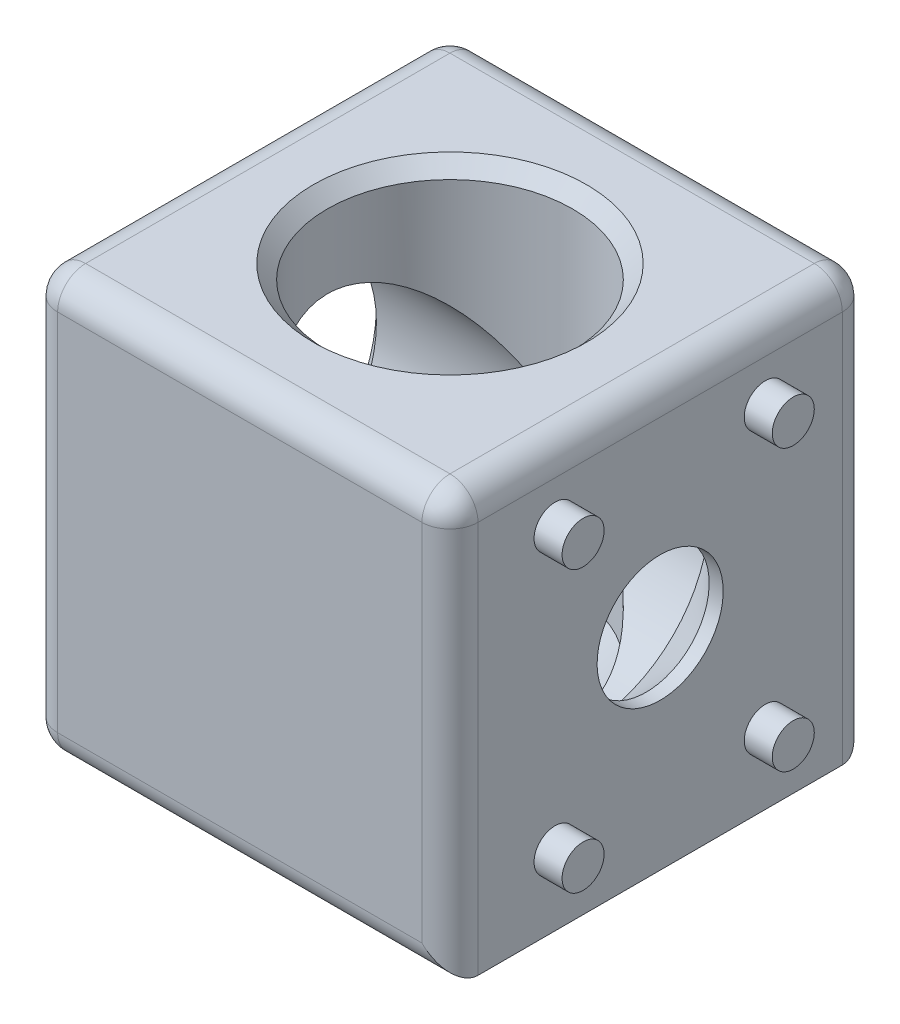
SolidWorks part; units mm, degrees
material "Алюминиевый сплав"
ref_plane "Спереди" through (0, 0, 0) normal (0, 0, 1) x (1, 0, 0)
ref_plane "Сверху" through (0, 0, 0) normal (0, 1, 0) x (1, 0, 0)
ref_plane "Справа" through (0, 0, 0) normal (1, 0, 0) x (0, 0, -1)
sketch "Эскиз1" plane through (0, 0, 0) normal (0, 1, 0) x (1, 0, 0)
  line L1 (-15, -15) -> (15, -15)
  line L2 (-15, -15) -> (-15, 15)
  line L3 (-15, 15) -> (15, 15)
  line L4 (15, -15) -> (15, 15)
  line L5 (-15, -15) -> (15, 15) construction
  line L6 (-15, 15) -> (15, -15) construction
  point P0 (0, 0)
  dimension "D1" = 30
extrude "Бобышка-Вытянуть1" add sketch "Эскиз1" along normal mid plane 30
sketch "Эскиз4" plane through (0, 0, 0) normal (0, 0, 1) x (1, 0, 0)
  line L0 (-4.5, -15) -> (-4.5, -14)
  line L1 (-15, -15) -> (15, -15) construction
  line L2 (-4.5, -14) -> (-8.75, -9.75)
  line L3 (-8.75, -9.75) -> (-8.75, 14)
  line L4 (-15, 15) -> (15, 15) construction
  line L6 (0, 15) -> (0, -15) construction
  line L7 (0, -15) -> (-4.5, -15)
  line L8 (0, 15) -> (0, -15)
  line L9 (-8.75, 14) -> (-9.75, 15)
  line L10 (-9.75, 15) -> (0, 15)
  dimension "D1" = 9
  dimension "D2" = 45
  dimension "D3" = 17.5
  dimension "D4" = 1
  dimension "D5" = 1
revolve "Вырез-Повернуть1" cut sketch "Эскиз4" angle 360 about L6
sketch "Эскиз5" plane through (0, -15, 0) normal (0, -1, 0) x (1, 0, 0)
  line L1 (-10, 7.5) -> (10, 7.5) construction
  line L2 (-10, 7.5) -> (-10, -7.5) construction
  line L3 (-10, -7.5) -> (10, -7.5) construction
  line L4 (10, 7.5) -> (10, -7.5) construction
  circle A0 centre (-10, 7.5) radius 1.5
  circle A1 centre (-10, -7.5) radius 1.5
  circle A2 centre (10, -7.5) radius 1.5
  circle A3 centre (10, 7.5) radius 1.5
  point P5 (-10, 0)
  point P12 (0, 7.5)
  dimension "D1" = 3
  dimension "D2" = 20
  dimension "D3" = 15
extrude "Бобышка-Вытянуть2" add sketch "Эскиз5" along normal blind 2
ref_plane "Плоскость1" through (0, 0, 0) normal (0.7071, 0.7071, 0) x (0.7071, -0.7071, 0)
mirror "Зеркальное отражение1" about plane through (0, 0, 0) normal (0.7071, 0.7071, 0) of "Бобышка-Вытянуть2", "Вырез-Повернуть1"
fillet "Скругление1" radius 2 11 edges at (-15, -15, 0) (15, 15, 0) (-15, 0, 15) (0, 15, 15) (-15, 15, 0) (-15, 0, -15) (0, 15, -15) (0, -15, -15) (15, 0, -15) (0, -15, 15) (15, 0, 15)
